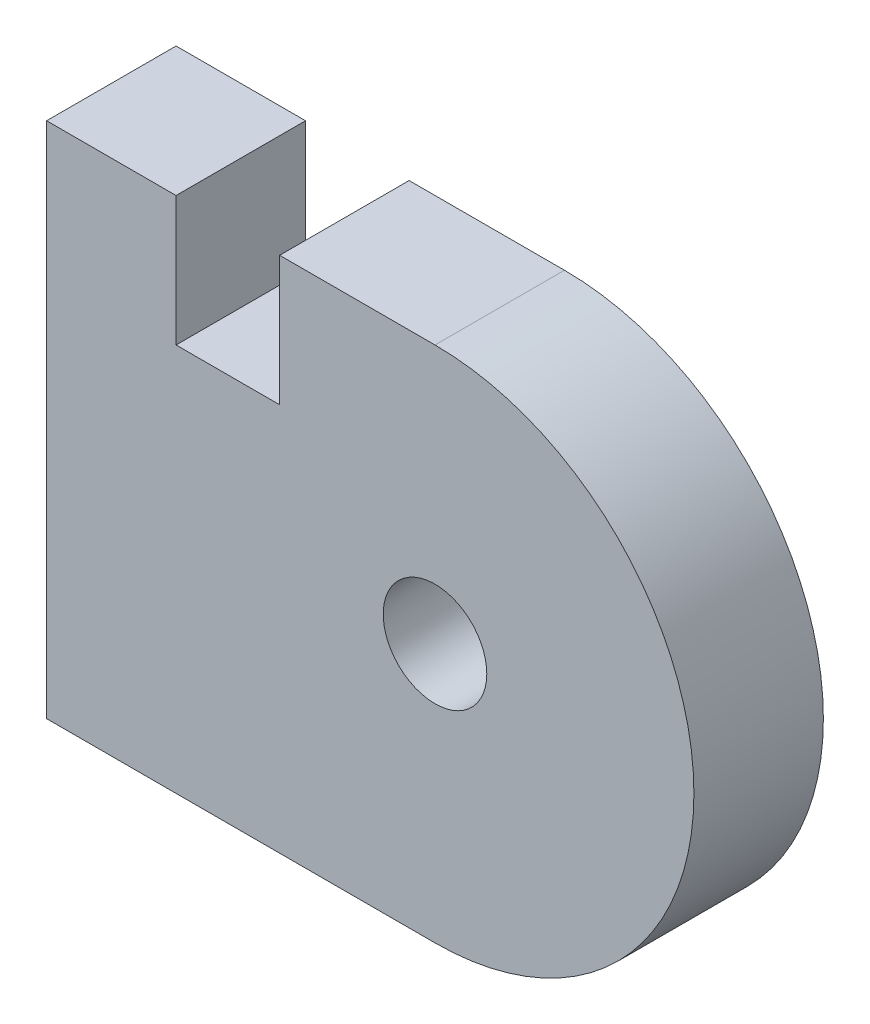
SolidWorks part; units mm, degrees
ref_plane "Front Plane" through (0, 0, 0) normal (0, 0, 1) x (1, 0, 0)
ref_plane "Top Plane" through (0, 0, 0) normal (0, 1, 0) x (1, 0, 0)
ref_plane "Right Plane" through (0, 0, 0) normal (1, 0, 0) x (0, 0, -1)
sketch "Sketch1" plane through (0, 0, 0) normal (0, 0, 1) x (1, 0, 0)
  line L0 (-3.5, 10) -> (2.5, 10)
  line L1 (-12.5, -10) -> (2.5, -10)
  line L3 (-3.5, 5) -> (-7.5, 5)
  line L6 (-7.5, 5) -> (-7.5, 10)
  line L7 (-7.5, 10) -> (-12.5, 10)
  line L8 (-12.5, 5) -> (-12.5, 10)
  line L9 (-3.5, 10) -> (-3.5, 5)
  line L10 (-12.5, 5) -> (-12.5, -10)
  arc A0 (2.5, -10) -> (2.5, 10) centre (2.5, 0) ccw
  circle A1 centre (2.5, 0) radius 2
extrude "Boss-Extrude1" add sketch "Sketch1" along normal blind 5
